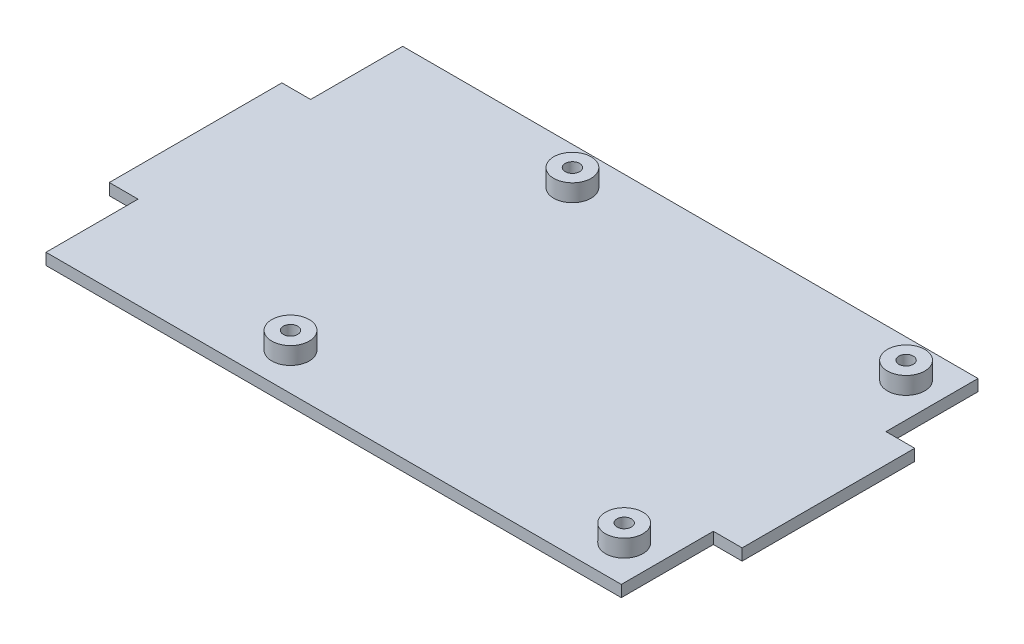
SolidWorks part; units mm, degrees
ref_plane "前视基准面" through (0, 0, 0) normal (0, 0, 1) x (1, 0, 0)
ref_plane "上视基准面" through (0, 0, 0) normal (0, 1, 0) x (1, 0, 0)
ref_plane "右视基准面" through (0, 0, 0) normal (1, 0, 0) x (0, 0, -1)
sketch "草图1" plane through (0, 0, 0) normal (0, 1, 0) x (1, 0, 0)
  line L1 (-50, 31) -> (50, 31)
  line L2 (-50, 31) -> (-50, -31)
  line L3 (-50, -31) -> (50, -31)
  line L4 (50, 31) -> (50, -31)
  line L5 (-50, 31) -> (50, -31) construction
  line L6 (-50, -31) -> (50, 31) construction
  line L7 (-55, 15) -> (55, 15)
  line L8 (-55, 15) -> (-55, -15)
  line L9 (-55, -15) -> (55, -15)
  line L10 (55, 15) -> (55, -15)
  line L11 (-55, 15) -> (55, -15) construction
  line L12 (-55, -15) -> (55, 15) construction
  point P0 (0, 0)
  point P6 (0, 0)
  dimension "D1" = 62
  dimension "D2" = 100
  dimension "D3" = 110
  dimension "D4" = 30
extrude "底板" add sketch "草图1" along normal blind 2 contours L8 L9 L10 L7 | L1 L4 L3 L2
sketch "草图2" plane through (0, 2, 0) normal (0, 1, 0) x (1, 0, 0)
  line L1 (-14, 24.5) -> (44, 24.5)
  line L2 (-14, 24.5) -> (-14, -24.5)
  line L3 (-14, -24.5) -> (44, -24.5)
  line L4 (44, 24.5) -> (44, -24.5)
  circle A0 centre (-14, 24.5) radius 1.25
  circle A1 centre (44, 24.5) radius 1.25
  circle A2 centre (-14, -24.5) radius 1.25
  circle A3 centre (44, -24.5) radius 1.25
  point P0 (0, 0)
  dimension "D3" = 2.5
  dimension "D4" = 2.5
  dimension "D5" = 2.5
  dimension "D6" = 2.5
  dimension "D1" = 49
  dimension "D2" = 58
  dimension "D7" = 44
extrude "螺丝孔" cut sketch "草图2" against normal blind 2 contours A0 | A2 | A3 | A1
sketch "草图3" plane through (0, 2, 0) normal (0, 1, 0) x (1, 0, 0)
  circle A0 centre (-14, 24.5) radius 1.25 construction
  circle A1 centre (-14, 24.5) radius 1.25
  circle A2 centre (44, 24.5) radius 1.25 construction
  circle A3 centre (44, 24.5) radius 1.25
  circle A4 centre (-14, -24.5) radius 1.25 construction
  circle A5 centre (-14, -24.5) radius 1.25
  circle A6 centre (44, -24.5) radius 1.25 construction
  circle A7 centre (44, -24.5) radius 1.25
  circle A8 centre (-14, 24.5) radius 3.25
  circle A9 centre (44, 24.5) radius 3.25
  circle A10 centre (-14, -24.5) radius 3.25
  circle A11 centre (44, -24.5) radius 3.25
  dimension "D1" = 2
extrude "螺丝架起" add sketch "草图3" along normal blind 3
